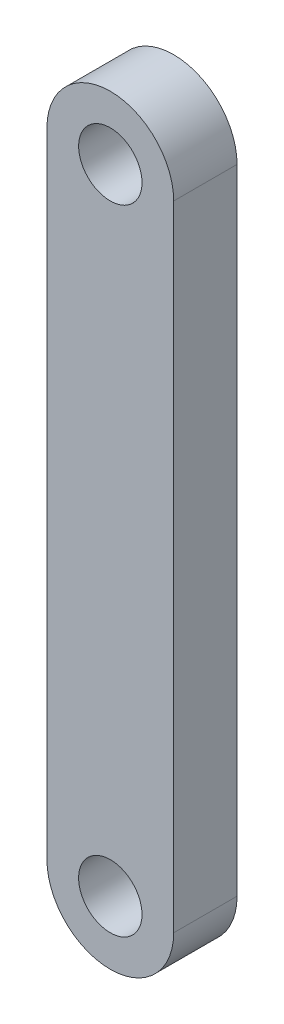
SolidWorks part; units mm, degrees
ref_plane "Front Plane" through (0, 0, 0) normal (0, 0, 1) x (1, 0, 0)
ref_plane "Top Plane" through (0, 0, 0) normal (0, 1, 0) x (1, 0, 0)
ref_plane "Right Plane" through (0, 0, 0) normal (1, 0, 0) x (0, 0, -1)
sketch "Sketch1" plane through (0, 0, 0) normal (0, 0, 1) x (1, 0, 0)
  line L0 (0, 0) -> (0, 63.5) construction
  line L1 (-6.35, 63.5) -> (-6.35, 0)
  line L2 (6.35, 63.5) -> (6.35, 0)
  arc A0 (-6.35, 0) -> (6.35, 0) centre (0, 0) ccw
  circle A1 centre (0, 0) radius 3.175
  circle A2 centre (0, 63.5) radius 3.175
  arc A3 (6.35, 63.5) -> (-6.35, 63.5) centre (0, 63.5) ccw
  dimension "D1" = 63.5
  dimension "D2" = 12.7
  dimension "D3" = 6.35
extrude "Boss-Extrude1" add sketch "Sketch1" along normal blind 6.35
